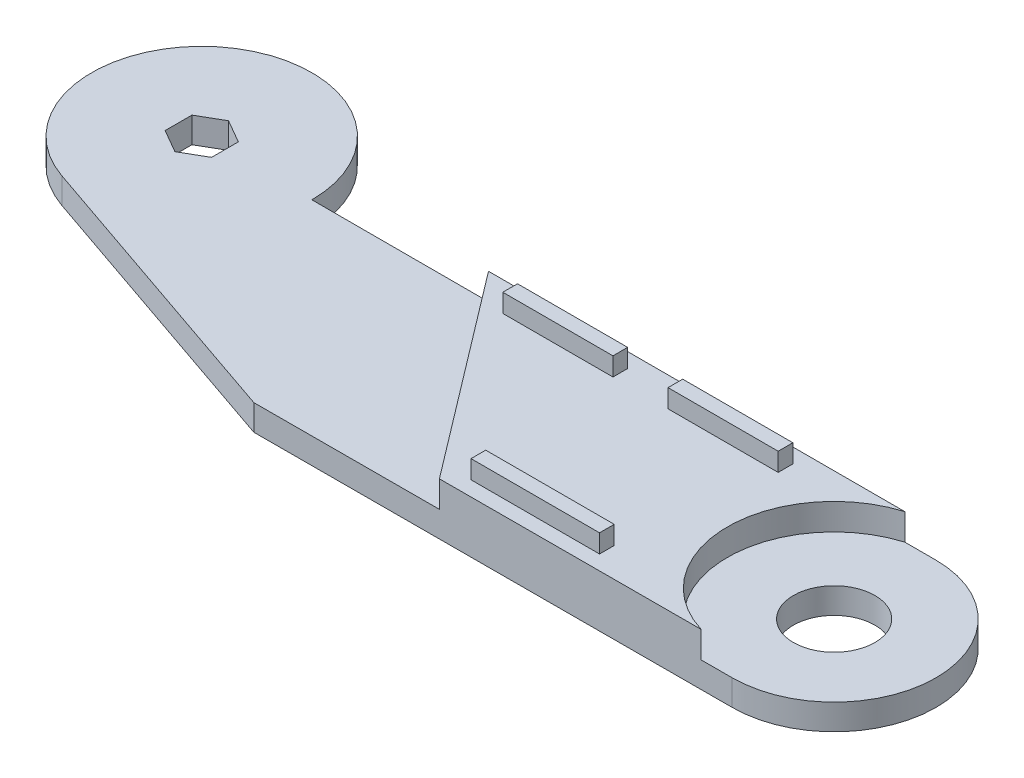
SolidWorks part; units mm, degrees
ref_plane "Front Plane" through (0, 0, 0) normal (0, 0, 1) x (1, 0, 0)
ref_plane "Top Plane" through (0, 0, 0) normal (0, 1, 0) x (1, 0, 0)
ref_plane "Right Plane" through (0, 0, 0) normal (1, 0, 0) x (0, 0, -1)
sketch "Эскиз1" plane through (0, 0, 0) normal (0, 1, 0) x (1, 0, 0)
  line L0 (69.9181, -55.7385) -> (-9.7464, -28.3727)
  line L3 (199.9178, -55.4999) -> (199.9178, 0)
  line L4 (199.9178, 0) -> (0, 0)
  line L5 (0, -30) -> (0, 0)
  line L6 (0, 0) -> (75, 0) construction
  line L7 (199.9178, -55.4999) -> (69.9181, -55.7385)
  circle A2 centre (200, -27.75) radius 27.75
  circle A4 centre (0, 0) radius 30
  dimension "D1" = 130
  dimension "D3" = 55.5
  dimension "D5" = 60
  dimension "D2" = 199.9178
  dimension "D6" = 75
extrude "Бобышка-Вытянуть1" add sketch "Эскиз1" along normal blind 7
sketch "Эскиз10" plane through (0, 0, 0) normal (0, -1, 0) x (1, 0, 0)
  line L1 (0, 7.3) -> (-6.322, 3.65)
  line L2 (-6.322, 3.65) -> (-6.322, -3.65)
  line L3 (-6.322, -3.65) -> (0, -7.3)
  line L4 (0, -7.3) -> (6.322, -3.65)
  line L5 (6.322, -3.65) -> (6.322, 3.65)
  line L6 (6.322, 3.65) -> (0, 7.3)
  circle A0 centre (0, 0) radius 6.322 construction
  point P0 (0, 0)
  dimension "D1" = 14.6
extrude "Вырез-Вытянуть1" cut sketch "Эскиз10" against normal blind 9
sketch "Эскиз11" plane through (0, 7, 0) normal (0, 1, 0) x (1, 0, 0)
  line L0 (199.9178, -55.4999) -> (69.9181, -55.7385) construction
  line L1 (199.9185, -55.4999) -> (199.9185, 0)
  line L2 (199.9178, 0) -> (30, 0) construction
  line L3 (199.9185, 0) -> (199.9178, -0.0001)
  line L4 (199.9185, -55.4999) -> (199.9178, -55.4999)
  line L5 (199.9185, -55.4999) -> (69.9185, -55.7385)
  line L6 (69.9185, -55.7385) -> (69.9185, 0)
  line L7 (69.9185, 0) -> (199.9185, 0)
  line L8 (69.9185, -55.7648) -> (69.9185, 0)
  circle A1 centre (199.9185, -27.7499) radius 29
  line M10 (69.9181, -55.7385) -> (199.9178, -55.4999)
  dimension "D1" = 130
  dimension "D2" = 58
extrude "Бобышка-Вытянуть5" add sketch "Эскиз11" along normal blind 7.2 contours A1 L7 L6 M10
sketch "Эскиз14" plane through (0, 0, 0) normal (0, -1, 0) x (1, 0, 0)
  circle A0 centre (200, 27.75) radius 11.1
  dimension "D1" = 22.2
extrude "Вырез-Вытянуть2" cut sketch "Эскиз14" against normal through all
sketch "Эскиз15" plane through (0, 14.2, 0) normal (0, 1, 0) x (1, 0, 0)
  line L0 (191.4959, 0) -> (69.9185, 0) construction
  line L1 (90, -4) -> (120, -4)
  line L2 (90, -4) -> (90, -8)
  line L3 (90, -8) -> (120, -8)
  line L4 (120, -4) -> (120, -8)
  line L5 (135, -4) -> (165, -4)
  line L6 (135, -4) -> (135, -8)
  line L7 (135, -8) -> (165, -8)
  line L8 (165, -4) -> (165, -8)
  line L13 (124.92, -47.5733) -> (159.92, -47.5733)
  line L14 (124.92, -47.5733) -> (124.92, -51.5733)
  line L15 (124.92, -51.5733) -> (159.92, -51.5733)
  line L16 (159.92, -47.5733) -> (159.92, -51.5733)
  line L18 (69.9185, -55.7385) -> (191.5467, -55.5152) construction
  dimension "D1" = 4
  dimension "D2" = 4
  dimension "D4" = 4
  dimension "D5" = 90
  dimension "D7" = 30
  dimension "D8" = 30
  dimension "D9" = 35
  dimension "D12" = 15
  dimension "D14" = 4
  dimension "D15" = 4
  dimension "D16" = 4
  dimension "D17" = 124.92
extrude "Бобышка-Вытянуть6" add sketch "Эскиз15" along normal blind 5
sketch "Эскиз16" plane through (0, 14.2, 0) normal (0, 1, 0) x (1, 0, 0)
  line L3 (191.4959, 0) -> (69.9185, 0) construction
  line L4 (78.1004, 0) -> (69.9185, 0)
  line L5 (69.9185, 0) -> (69.9185, -55.7385)
  line L7 (78.1004, 0) -> (120.375, -55.6459)
  line L8 (69.9185, -55.7385) -> (191.5467, -55.5152) construction
  line L9 (120.375, -55.6459) -> (69.9185, -55.7385)
extrude "Вырез-Вытянуть3" cut sketch "Эскиз16" against normal blind 7.2
